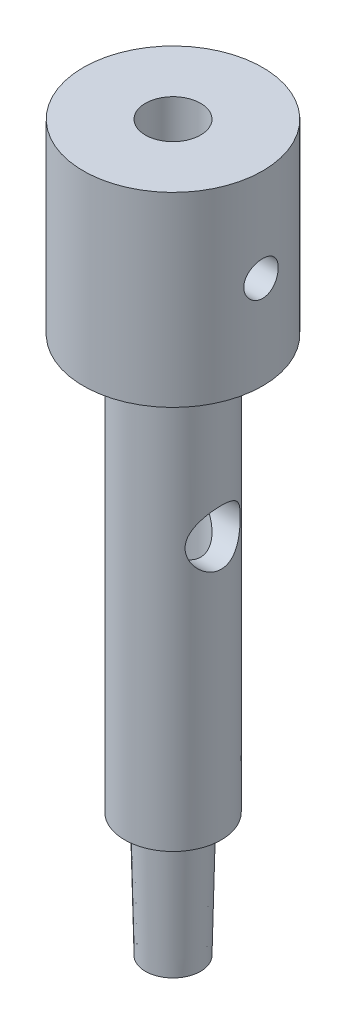
SolidWorks part; units mm, degrees
material "Латунь"
ref_plane "Спереди" through (0, 0, 0) normal (0, 0, 1) x (1, 0, 0)
ref_plane "Сверху" through (0, 0, 0) normal (0, 1, 0) x (1, 0, 0)
ref_plane "Справа" through (0, 0, 0) normal (1, 0, 0) x (0, 0, -1)
sketch "Эскиз1" plane through (0, 0, 0) normal (0, 0, 1) x (1, 0, 0)
  line L0 (0, 17.7192) -> (0, -34.7808) construction
  line L1 (-2, -34.7808) -> (-1.25, -34.7808)
  line L2 (-6.5, 17.7192) -> (-6.5, 4.2192)
  line L3 (-6.5, 4.2192) -> (-3.5, 4.2192)
  line L4 (-3.5, 4.2192) -> (-3.5, -25.7808)
  line L5 (-3.5, -25.7808) -> (-2.2, -25.7808)
  line L6 (-2.2, -25.7808) -> (-2, -34.7808)
  line L7 (-1.25, -34.7808) -> (-1.25, -19.2315)
  line L8 (-1.25, -19.2315) -> (-2, -18.7808)
  line L9 (-2, -18.7808) -> (-2, 17.7192)
  line L10 (-2, 17.7192) -> (-6.5, 17.7192)
  line L11 (-1.25, -19.2315) -> (0, -19.9825) construction
  line L12 (0, -19.9825) -> (1.25, -19.2315) construction
  line L14 (-6.5, -20.7808) -> (6.5, -20.7808) construction
  dimension "D1" = 2.2
  dimension "D2" = 2
  dimension "D3" = 3.5
  dimension "D4" = 2.5
  dimension "D5" = 2
  dimension "D6" = 6.5
  dimension "D7" = 13.5
  dimension "D8" = 9
  dimension "D9" = 5
  dimension "D10" = 17.7192
  dimension "D11" = 7
  dimension "D12" = 118
revolve "Повернуть1" add sketch "Эскиз1" angle 360 about L0
ref_plane "Плоскость1" through (3.5, 0, 0) normal (1, 0, 0) x (0, 0, -1)
sketch "Эскиз2" plane through (3.5, 0, 0) normal (1, 0, 0) x (0, 0, -1)
  line L0 (0, 4.2192) -> (0, -25.7808) construction
  line L1 (-3.5, 4.2192) -> (3.5, 4.2192) construction
  line L2 (-2.2, -25.7808) -> (2.2, -25.7808) construction
  line L3 (-6.5, -20.7808) -> (6.5, -20.7808) construction
  circle A0 centre (0, -6.7808) radius 2
  dimension "D1" = 4
  dimension "D2" = 14
extrude "Вырез-Вытянуть1" cut sketch "Эскиз2" against normal blind 3.5
ref_plane "Плоскость2" through (6.5, 0, 0) normal (1, 0, 0) x (0, 0, -1)
sketch "Эскиз3" plane through (6.5, 0, 0) normal (1, 0, 0) x (0, 0, -1)
  line L0 (0, 17.7192) -> (0, 4.2192) construction
  line L1 (6.5, 17.7192) -> (-6.5, 17.7192) construction
  line L2 (-6.5, 4.2192) -> (6.5, 4.2192) construction
  point P6 (0, 10.9692)
hole_wizard "Отверстие обработанное метчиком M31" positions "Эскиз5" profile "Эскиз4" tap size "M3" standard "DIN"
sketch "Эскиз5" plane through (6.5, 0, 0) normal (1, 0, 0) x (0, 0, -1)
  point P0 (0, 10.9692)
sketch "Эскиз4" plane through (6.5, 10.9692, 0) normal (0, 1, 0) x (0, 0, -1)
  line L0 (0, 0) -> (0, 6.7511)
  line L1 (0, 6.7511) -> (1.25, 6)
  line L2 (1.25, 6) -> (1.25, 0)
  line L5 (1.25, 0) -> (0, 0)
  line L10 (0, 6.7511) -> (-1.25, 6) construction
  line L11 (0, -6.35) -> (0, 107.95) construction
  dimension "Диаметр сверла" = 2.5
  dimension "Глубина сверла" = 6
  dimension "Угол заточки сверла" = 118
cosmetic thread "Отверстие резьбы1" parameters "D1"=4.9388, "D2"=3
